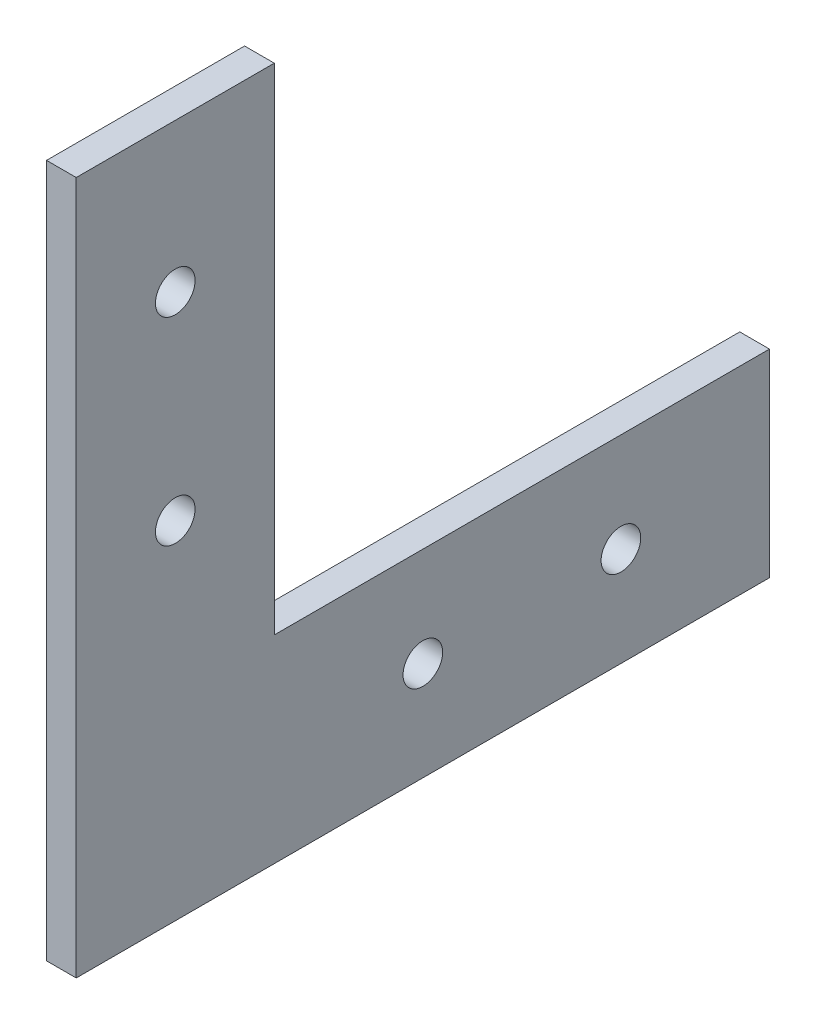
SolidWorks part; units mm, degrees
ref_plane "Plano frontal" through (0, 0, 0) normal (0, 0, 1) x (1, 0, 0)
ref_plane "Plano superior" through (0, 0, 0) normal (0, 1, 0) x (1, 0, 0)
ref_plane "Plano direito" through (0, 0, 0) normal (1, 0, 0) x (0, 0, -1)
sketch "Esboço1" plane through (0, 0, 0) normal (1, 0, 0) x (0, 0, -1)
  line L0 (70, 10) -> (-6.9254, 10) construction
  line L1 (0, 0) -> (20, 0)
  line L2 (0, 0) -> (0, 70)
  line L3 (0, 70) -> (20, 70)
  line L4 (20, 0) -> (20, 70)
  line L5 (0, 0) -> (70, 0)
  line L6 (0, 0) -> (0, 20)
  line L7 (0, 20) -> (70, 20)
  line L8 (70, 0) -> (70, 20)
  line L9 (10, 70) -> (10, -8.937) construction
  circle A0 centre (55, 10) radius 2
  circle A1 centre (35, 10) radius 2
  circle A2 centre (10, 35) radius 2
  circle A3 centre (10, 55) radius 2
  dimension "D5" = 4
  dimension "D6" = 4
  dimension "D7" = 4
  dimension "D8" = 4
  dimension "D1" = 70
  dimension "D2" = 70
  dimension "D3" = 20
  dimension "D4" = 20
  dimension "D9" = 20
  dimension "D10" = 15
  dimension "D11" = 20
  dimension "D12" = 15
extrude "Ressalto-extrusão1" add sketch "Esboço1" along normal blind 3 contours L2 L7 L4 L3 A3 A2 | L5 L8 L7 L4 A1 A0 | L7 L2 L1 L4
equation "\"D6@Esboço1\"=\"D5@Esboço1\""
equation "\"D7@Esboço1\"=\"D6@Esboço1\""
equation "\"D8@Esboço1\"=\"D5@Esboço1\""
equation "\"D3@Esboço1\"=\"D4@Esboço1\""
equation "\"D1@Esboço1\"=\"D2@Esboço1\""
equation "\"D11@Esboço1\"=\"D9@Esboço1\""
equation "\"D12@Esboço1\"=\"D10@Esboço1\""
